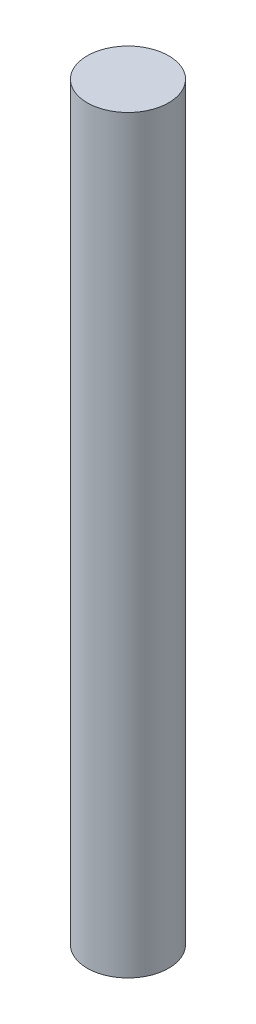
SolidWorks part; units mm, degrees
ref_plane "Alzado" through (0, 0, 0) normal (0, 0, 1) x (1, 0, 0)
ref_plane "Planta" through (0, 0, 0) normal (0, 1, 0) x (1, 0, 0)
ref_plane "Vista lateral" through (0, 0, 0) normal (1, 0, 0) x (0, 0, -1)
sketch "Croquis1" plane through (0, 0, 0) normal (0, 1, 0) x (1, 0, 0)
  circle A0 centre (0, 0) radius 2.5
  dimension "D1" = 5
extrude "Saliente-Extruir1" add sketch "Croquis1" along normal blind 46
